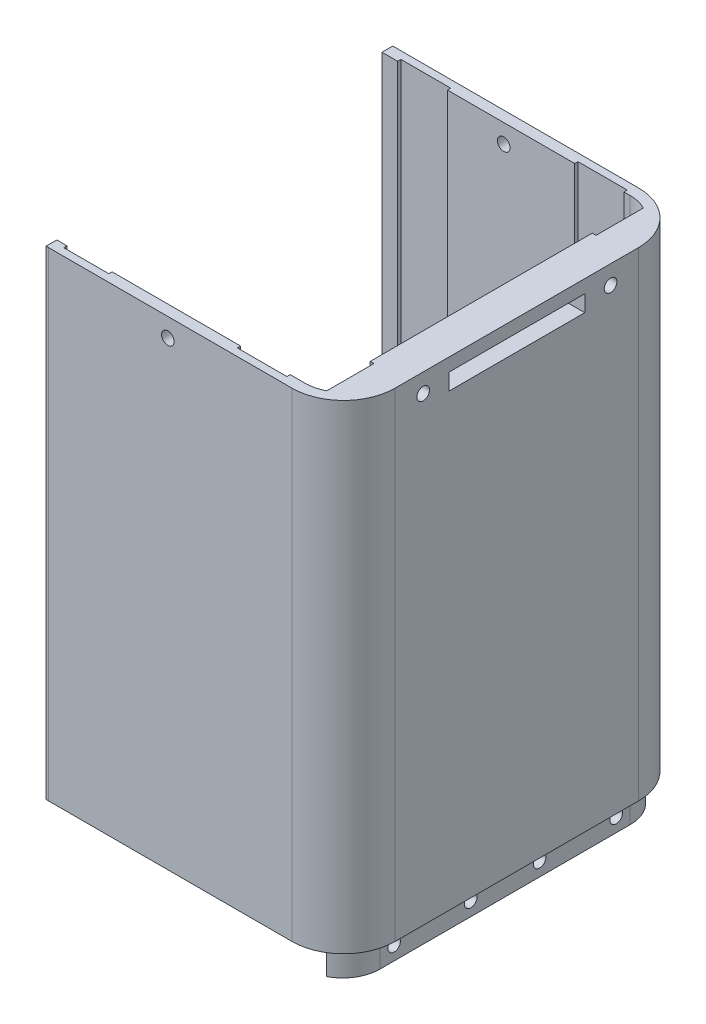
SolidWorks part; units mm, degrees
ref_plane "Front Plane" through (0, 0, 0) normal (0, 0, 1) x (1, 0, 0)
ref_plane "Top Plane" through (0, 0, 0) normal (0, 1, 0) x (1, 0, 0)
ref_plane "Right Plane" through (0, 0, 0) normal (1, 0, 0) x (0, 0, -1)
sketch "Sketch1" plane through (0, 0, 0) normal (0, 1, 0) x (1, 0, 0)
  line L0 (-45.3131, -33.5853) -> (-45.3131, -31.2966)
  line L1 (-53.3131, -23.2966) -> (-53.3131, 30.1034)
  line L2 (-45.3131, 38.1034) -> (-45.3131, 40.392)
  line L3 (-55.8131, 29.4034) -> (-55.8131, -22.5966)
  line L4 (-45.3131, 38.1034) -> (7.6869, 38.1034)
  line L5 (15.6869, 30.1034) -> (15.6869, -23.2966)
  line L6 (7.6869, -31.2966) -> (-45.3131, -31.2966)
  line L7 (-45.3131, -31.2966) -> (-45.3131, -33.5853)
  line L8 (-44.8131, -33.5966) -> (7.1869, -33.5966)
  line L9 (18.1869, -22.5966) -> (18.1869, 29.4034)
  line L10 (7.1869, 40.4034) -> (-45.3131, 40.4034)
  line L11 (-45.3131, 40.4034) -> (-45.3131, 38.1034)
  arc A0 (-53.3131, -23.2966) -> (-45.3131, -31.2966) centre (-45.3131, -23.2966) ccw
  arc A1 (-45.3131, 38.1034) -> (-53.3131, 30.1034) centre (-45.3131, 30.1034) ccw
  arc A2 (-45.3131, 40.392) -> (-55.8131, 29.4034) centre (-44.8131, 29.4034) ccw
  arc A3 (-55.8131, -22.5966) -> (-45.3131, -33.5853) centre (-44.8131, -22.5966) ccw
  arc A4 (15.6869, 30.1034) -> (7.6869, 38.1034) centre (7.6869, 30.1034) ccw
  arc A5 (7.6869, -31.2966) -> (15.6869, -23.2966) centre (7.6869, -23.2966) ccw
  arc A6 (-45.3131, -33.5853) -> (-44.8131, -33.5966) centre (-44.8131, -22.5966) ccw
  arc A7 (7.1869, -33.5966) -> (18.1869, -22.5966) centre (7.1869, -22.5966) ccw
  arc A8 (18.1869, 29.4034) -> (7.1869, 40.4034) centre (7.1869, 29.4034) ccw
extrude "Boss-Extrude1" add sketch "Sketch1" along normal blind 120 contours L3 A3 L0 A0 L1 A1 L2 A2 | L9 A8 L10 L11 L2 L4 A4 L5 A5 L6 L0 A6 L8 A7
sketch "Sketch3" plane through (0, 0, 0) normal (0, -1, 0) x (1, 0, 0)
  line L0 (-49.0131, 31.9727) -> (-49.0131, -37.6232)
  line L1 (-49.0131, -37.6232) -> (-53.3365, -34.9139)
  line L2 (-53.3365, -34.9139) -> (-55.1111, -29.9846)
  line L3 (-55.1111, -29.9846) -> (-55.1111, -26.8112)
  line L4 (-55.1111, -26.8112) -> (-55.1111, 25.4524)
  line L5 (-55.1111, 25.4524) -> (-53.6528, 27.7793)
  line L6 (-53.6528, 27.7793) -> (-52.0732, 30.2267)
  line L7 (-52.0732, 30.2267) -> (-49.0131, 31.9727)
  line L8 (11.3869, 31.9727) -> (11.3869, -38.4878)
  line L9 (11.3869, -38.4878) -> (13.2697, -37.81)
  line L10 (13.2697, -37.81) -> (16.7371, -32.277)
  line L11 (16.7371, -32.277) -> (16.5683, -31.171)
  line L12 (16.5683, -31.171) -> (16.5683, 24.7898)
  line L13 (16.5683, 24.7898) -> (15.0385, 28.9972)
  line L14 (15.0385, 28.9972) -> (11.3869, 31.9727)
  line L15 (15.6869, -30.1034) -> (15.6869, 23.2966) construction
  line L16 (-53.3131, 23.2966) -> (-53.3131, -30.1034) construction
  dimension "D1" = 4.3
  dimension "D2" = 4.3
extrude "Boss-Extrude2" add sketch "Sketch3" against normal up to surface (120 mm away) up to face at (-18.8131, 120, -3.4034)
sketch "Sketch4" plane through (0, 0, 0) normal (0, -1, 0) x (1, 0, 0)
  line L0 (11.3869, 30.3896) -> (11.3869, -37.1963) construction
  line L1 (11.3869, 20.2966) -> (10.5869, 20.2966)
  line L2 (11.3869, 20.2966) -> (11.3869, -27.1034)
  line L3 (11.3869, -27.1034) -> (10.5869, -27.1034)
  line L4 (10.5869, 20.2966) -> (10.5869, -27.1034)
  line L5 (-45.3131, -38.1034) -> (7.6869, -38.1034) construction
  line L6 (7.6869, 31.2966) -> (-45.3131, 31.2966) construction
  line L7 (-49.0131, -37.1963) -> (-49.0131, 30.3896) construction
  line L8 (-49.0131, 20.2966) -> (-48.2131, 20.2966)
  line L9 (-49.0131, 20.2966) -> (-49.0131, -27.1034)
  line L10 (-49.0131, -27.1034) -> (-48.2131, -27.1034)
  line L11 (-48.2131, 20.2966) -> (-48.2131, -27.1034)
  dimension "D1" = 0.8
  dimension "D2" = 11
  dimension "D3" = 11
  dimension "D4" = 0.8
  dimension "D5" = 11
  dimension "D6" = 11
extrude "Boss-Extrude3" add sketch "Sketch4" against normal up to surface (120 mm away) up to face at (-18.8131, 120, -3.4034)
sketch "Sketch5" plane through (0, 0, 0) normal (0, -1, 0) x (1, 0, 0)
  line L0 (-53.3131, 23.2966) -> (-53.3131, -30.1034) construction
  line L1 (15.6869, -30.1034) -> (15.6869, 23.2966) construction
  line L2 (-53.3131, 23.2966) -> (-53.3131, -30.1034)
  line L3 (15.6869, -30.1034) -> (15.6869, 23.2966)
  line L5 (-55.8131, 22.5966) -> (-55.8131, -29.4034)
  line L6 (-45.3131, -40.392) -> (-45.3131, -40.4034)
  line L7 (-45.3131, -40.4034) -> (7.1869, -40.4034)
  line L8 (18.1869, -29.4034) -> (18.1869, 22.5966)
  line L9 (7.1869, 33.5966) -> (-44.8131, 33.5966)
  line L10 (-55.8131, 22.5966) -> (-55.8131, -29.4034)
  line L11 (-45.3131, -40.392) -> (-45.3131, -40.4034)
  line L12 (-45.3131, -40.4034) -> (7.1869, -40.4034)
  line L13 (18.1869, -29.4034) -> (18.1869, 22.5966)
  line L14 (7.1869, 33.5966) -> (-44.8131, 33.5966)
  arc A0 (-45.3131, 31.2966) -> (-53.3131, 23.2966) centre (-45.3131, 23.2966) ccw construction
  arc A1 (-53.3131, -30.1034) -> (-45.3131, -38.1034) centre (-45.3131, -30.1034) ccw construction
  arc A2 (7.6869, -38.1034) -> (15.6869, -30.1034) centre (7.6869, -30.1034) ccw construction
  arc A3 (15.6869, 23.2966) -> (7.6869, 31.2966) centre (7.6869, 23.2966) ccw construction
  arc A4 (-55.8131, -29.4034) -> (-45.3131, -40.392) centre (-44.8131, -29.4034) ccw
  arc A5 (7.1869, -40.4034) -> (18.1869, -29.4034) centre (7.1869, -29.4034) ccw
  arc A6 (18.1869, 22.5966) -> (7.1869, 33.5966) centre (7.1869, 22.5966) ccw
  arc A7 (-44.8131, 33.5966) -> (-55.8131, 22.5966) centre (-44.8131, 22.5966) ccw
  arc A8 (-55.8131, -29.4034) -> (-45.3131, -40.392) centre (-44.8131, -29.4034) ccw
  arc A9 (7.1869, -40.4034) -> (18.1869, -29.4034) centre (7.1869, -29.4034) ccw
  arc A10 (18.1869, 22.5966) -> (7.1869, 33.5966) centre (7.1869, 22.5966) ccw
  arc A11 (-44.8131, 33.5966) -> (-55.8131, 22.5966) centre (-44.8131, 22.5966) ccw
  arc A12 (-45.3131, 31.2966) -> (-53.3131, 23.2966) centre (-45.3131, 23.2966) ccw
  arc A13 (-53.3131, -30.1034) -> (-45.3131, -38.1034) centre (-45.3131, -30.1034) ccw
  arc A14 (7.6869, -38.1034) -> (15.6869, -30.1034) centre (7.6869, -30.1034) ccw
  arc A15 (15.6869, 23.2966) -> (7.6869, 31.2966) centre (7.6869, 23.2966) ccw
  line M10 (11.3869, 30.3896) -> (11.3869, 20.2966)
  line M11 (11.3869, 20.2966) -> (10.5869, 20.2966)
  line M12 (10.5869, 20.2966) -> (10.5869, -27.1034)
  line M13 (10.5869, -27.1034) -> (11.3869, -27.1034)
  line M14 (11.3869, -27.1034) -> (11.3869, -37.1963)
  line M18 (-49.0131, -37.1963) -> (-49.0131, -27.1034)
  line M19 (-49.0131, -27.1034) -> (-48.2131, -27.1034)
  line M20 (-48.2131, -27.1034) -> (-48.2131, 20.2966)
  line M21 (-48.2131, 20.2966) -> (-49.0131, 20.2966)
  line M22 (-49.0131, 20.2966) -> (-49.0131, 30.3896)
  dimension "D1" = 0
extrude "Boss-Extrude4" add sketch "Sketch5" along normal blind 6 contours L2 A13 A12 M18 M19 M20 M21 M22 | L3 A15 A14 M10 M11 M12 M13 M14
sketch "Sketch6" plane through (0, -6, 0) normal (0, -1, 0) x (1, 0, 0)
  line L0 (-48.2131, -27.1034) -> (-48.2131, 20.2966) construction
  line L1 (-47.5159, 17.2966) -> (-50.7131, 17.2966)
  line L2 (-47.5159, 17.2966) -> (-47.5159, 7.2966)
  line L3 (-47.5159, 7.2966) -> (-50.7131, 7.2966)
  line L4 (-50.7131, 17.2966) -> (-50.7131, 7.2966)
  line L5 (-48.1684, -14.1034) -> (-50.7131, -14.1034)
  line L6 (-48.1684, -14.1034) -> (-48.1684, -24.1034)
  line L7 (-48.1684, -24.1034) -> (-50.7131, -24.1034)
  line L8 (-50.7131, -14.1034) -> (-50.7131, -24.1034)
  line L9 (-48.2131, 20.2966) -> (-49.0131, 20.2966) construction
  line L10 (-49.0131, -27.1034) -> (-48.2131, -27.1034) construction
  line L11 (-18.8131, 54.1571) -> (-18.8131, -72.2254)
  line L12 (-55.8131, -29.4034) -> (-55.8131, 22.5966) construction
  line L13 (10.5422, -24.1034) -> (13.0869, -24.1034)
  line L14 (13.0869, -14.1034) -> (13.0869, -24.1034)
  line L15 (10.5422, -14.1034) -> (13.0869, -14.1034)
  line L16 (10.5422, -14.1034) -> (10.5422, -24.1034)
  line L17 (9.8897, 7.2966) -> (13.0869, 7.2966)
  line L18 (13.0869, 17.2966) -> (13.0869, 7.2966)
  line L19 (9.8897, 17.2966) -> (13.0869, 17.2966)
  line L20 (9.8897, 17.2966) -> (9.8897, 7.2966)
  dimension "D1" = 2.5
  dimension "D2" = 2.5
  dimension "D3" = 10
  dimension "D4" = 10
  dimension "D5" = 3
  dimension "D6" = 3
  dimension "D7" = 37
extrude "Cut-Extrude1" cut sketch "Sketch6" against normal blind 90 contours L2 L3 L4 L1 | L6 L7 L8 L5 | L14 L13 L16 L15 | L18 L17 L20 L19
sketch "Sketch7" plane through (0, -6, 0) normal (0, -1, 0) x (1, 0, 0)
  line L1 (-45.3131, 50.3412) -> (-63.8027, 50.3412)
  line L2 (-45.3131, 50.3412) -> (-45.3131, -69.8531)
  line L3 (-45.3131, -69.8531) -> (-63.8027, -69.8531)
  line L4 (-63.8027, 50.3412) -> (-63.8027, -69.8531)
  dimension "D1" = 0
extrude "Cut-Extrude2" cut sketch "Sketch7" against normal blind 140
sketch "Sketch9" plane through (10.5869, 0, 0) normal (-1, 0, 0) x (0, 0, 1)
  line L0 (7.2966, -6) -> (-14.1034, -6) construction
  line L1 (-7.4034, 19) -> (0.5966, 19)
  line L2 (-7.4034, 19) -> (-7.4034, -14.33)
  line L3 (-7.4034, -14.33) -> (0.5966, -14.33)
  line L4 (0.5966, 19) -> (0.5966, -14.33)
  line L5 (7.2966, 84) -> (7.2966, -6) construction
  dimension "D1" = 8
  dimension "D2" = 25
  dimension "D3" = 6.7
extrude "Cut-Extrude3" cut sketch "Sketch9" against normal blind 4
sketch "Sketch10" plane through (10.5869, 0, 0) normal (-1, 0, 0) x (0, 0, 1)
  line L1 (7.2966, 84) -> (7.2966, -6) construction
  line L2 (-14.1034, 84) -> (-14.1034, -6) construction
  line L3 (-7.4034, -6) -> (-14.1034, -6) construction
  line L4 (7.2966, -6) -> (0.5966, -6) construction
  circle A0 centre (-10.7534, -3) radius 1.35
  circle A1 centre (3.9466, -3) radius 1.35
  dimension "D1" = 3.35
  dimension "D2" = 3.35
  dimension "D3" = 3
  dimension "D4" = 3
  dimension "D5" = 2.7
  dimension "D6" = 2.7
extrude "Cut-Extrude4" cut sketch "Sketch10" against normal blind 11
sketch "Sketch11" plane through (10.5869, 0, 0) normal (-1, 0, 0) x (0, 0, 1)
  line L0 (30.3896, -6) -> (20.2966, -6) construction
  line L1 (17.2966, 84) -> (17.2966, -6) construction
  line L2 (-27.1034, 120) -> (-27.1034, -6) construction
  line L3 (-27.1034, -6) -> (-37.1963, -6) construction
  circle A0 centre (20.2966, -3) radius 1.35
  circle A1 centre (-27.1034, -3) radius 1.35
  dimension "D1" = 3
  dimension "D2" = 3
  dimension "D3" = 2.7
  dimension "D4" = 2.7
  dimension "D5" = 3
extrude "Cut-Extrude5" cut sketch "Sketch11" against normal blind 11
sketch "Sketch12" plane through (18.1869, 0, 0) normal (1, 0, 0) x (0, 0, -1)
  line L1 (17.9034, 99.5) -> (-11.0966, 99.5)
  line L2 (17.9034, 99.5) -> (17.9034, 96)
  line L3 (17.9034, 96) -> (-11.0966, 96)
  line L4 (-11.0966, 99.5) -> (-11.0966, 96)
extrude "Cut-Extrude6" cut sketch "Sketch12" against normal blind 10
sketch "Sketch13" plane through (18.1869, 0, 0) normal (1, 0, 0) x (0, 0, -1)
  line L0 (-11.0966, 99.3) -> (17.4034, 99.3) construction
  line L1 (48.9841, 102.3) -> (-44.2401, 102.3)
  line L2 (48.9841, 102.3) -> (48.9841, 126.272)
  line L3 (48.9841, 126.272) -> (-44.2401, 126.272)
  line L4 (-44.2401, 102.3) -> (-44.2401, 126.272)
  dimension "D1" = 3
extrude "Cut-Extrude7" cut sketch "Sketch13" against normal blind 103
sketch "Sketch14" plane through (10.5869, 0, 0) normal (-1, 0, 0) x (0, 0, 1)
  line L1 (17.2966, 84) -> (-21.409, 84)
  line L2 (17.2966, 84) -> (17.2966, 74)
  line L3 (17.2966, 74) -> (-21.409, 74)
  line L4 (-21.409, 84) -> (-21.409, 74)
  dimension "D1" = 10
extrude "Cut-Extrude8" cut sketch "Sketch14" against normal up to surface (2.5 mm away) up to face at (13.0869, 39, -19.1034)
sketch "Sketch15" plane through (18.1869, 0, 0) normal (1, 0, 0) x (0, 0, -1)
  line L0 (-22.5966, 102.3) -> (29.4034, 102.3) construction
  line L1 (29.4034, 102.3) -> (29.4034, 0) construction
  line L2 (-22.5966, 102.3) -> (-22.5966, 0) construction
  circle A0 centre (23.4034, 98.3) radius 1.35
  circle A1 centre (-16.5966, 98.3) radius 1.35
  dimension "D1" = 4
  dimension "D2" = 4
  dimension "D3" = 6
  dimension "D4" = 6
  dimension "D5" = 2.7
  dimension "D6" = 2.7
extrude "Cut-Extrude9" cut sketch "Sketch15" against normal blind 5
sketch "Sketch16" plane through (0, 0, 33.5966) normal (0, 0, 1) x (1, 0, 0)
  line L0 (7.1869, 102.3) -> (-44.8131, 102.3) construction
  line L1 (7.1869, 102.3) -> (7.1869, 0) construction
  circle A0 centre (-19.3131, 98.3) radius 1.35
  dimension "D1" = 2.7
  dimension "D2" = 4
  dimension "D3" = 26.5
extrude "Cut-Extrude10" cut sketch "Sketch16" against normal blind 88
sketch "Sketch17" plane through (0, 102.3, 0) normal (0, 1, 0) x (1, 0, 0)
  line L0 (7.6869, 38.1034) -> (-45.3131, 38.1034) construction
  line L1 (-41.9578, 38.8034) -> (-31.3326, 38.8034)
  line L2 (-41.9578, 38.8034) -> (-41.9578, 37.5993)
  line L3 (-41.9578, 37.5993) -> (-31.3326, 37.5993)
  line L4 (-31.3326, 38.8034) -> (-31.3326, 37.5993)
  line L5 (-45.3131, -31.2966) -> (7.6869, -31.2966) construction
  line L6 (-4.1574, 38.8034) -> (6.3505, 38.8034)
  line L7 (-4.1574, 38.8034) -> (-4.1574, 37.5993)
  line L8 (-4.1574, 37.5993) -> (6.3505, 37.5993)
  line L9 (6.3505, 38.8034) -> (6.3505, 37.5993)
  line L11 (-43.1618, -30.9911) -> (-33.5148, -30.9911)
  line L12 (-43.1618, -30.9911) -> (-43.1618, -31.9966)
  line L13 (-43.1618, -31.9966) -> (-33.5148, -31.9966)
  line L14 (-33.5148, -30.9911) -> (-33.5148, -31.9966)
  line L16 (-6.0915, -30.5513) -> (4.4845, -30.5513)
  line L17 (-6.0915, -30.5513) -> (-6.0915, -31.9966)
  line L18 (-6.0915, -31.9966) -> (4.4845, -31.9966)
  line L19 (4.4845, -30.5513) -> (4.4845, -31.9966)
  dimension "D1" = 0.7
  dimension "D2" = 0.7
  dimension "D3" = 0.7
extrude "Cut-Extrude11" cut sketch "Sketch17" against normal blind 200
